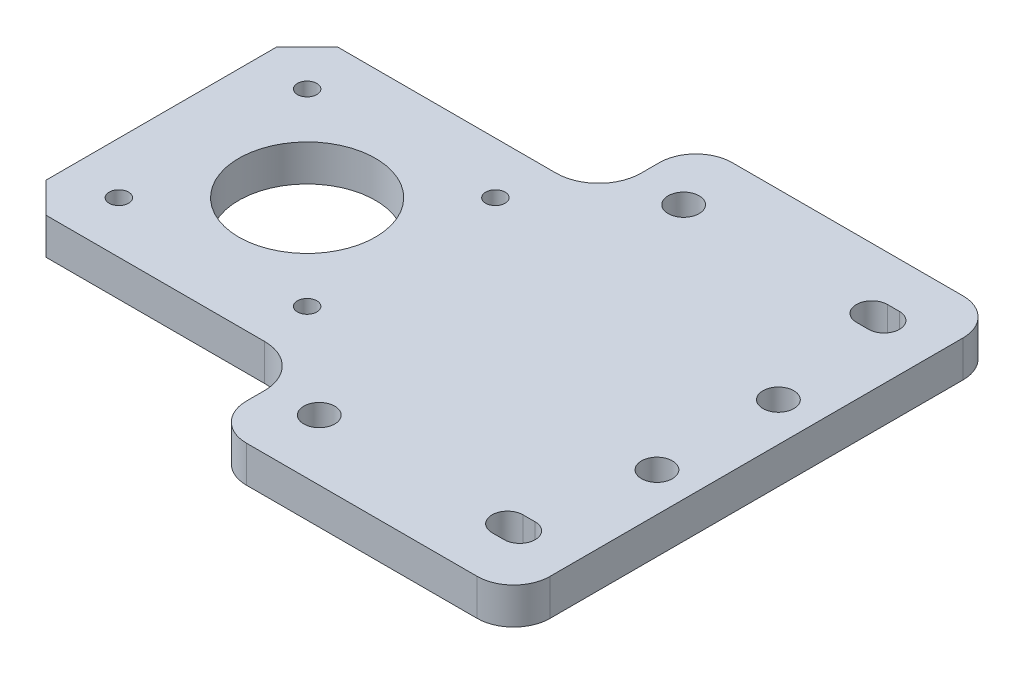
SolidWorks part; units mm, degrees
material "Клен"
ref_plane "Спереди" through (0, 0, 0) normal (0, 0, 1) x (1, 0, 0)
ref_plane "Сверху" through (0, 0, 0) normal (0, 1, 0) x (1, 0, 0)
ref_plane "Справа" through (0, 0, 0) normal (1, 0, 0) x (0, 0, -1)
sketch "Эскиз1" plane through (0, 0, 0) normal (0, 1, 0) x (1, 0, 0)
  line L0 (-56.8562, 0) -> (56.8562, 0) construction
  line L9 (-32, -24) -> (-68, -24)
  line L10 (-19, -40) -> (19, -40)
  line L11 (-25, -34) -> (-25, -31)
  line L12 (-19, 40) -> (19, 40)
  line L13 (25, -34) -> (25, 34)
  line L14 (-25, -40) -> (25, 40) construction
  line L15 (-25, 40) -> (25, -40) construction
  line L20 (-73, -19) -> (-73, 19)
  line L21 (-32, 24) -> (-68, 24)
  line L22 (-25, 31) -> (-25, 34)
  line L23 (-68, -24) -> (-73, -19)
  line L24 (-68, 24) -> (-73, 19)
  line L25 (-73, -24) -> (-25, 24) construction
  line L26 (-25, -24) -> (-72.5248, 23.5248) construction
  line L27 (-49, -29.3961) -> (-49, 34.1878) construction
  line L28 (12.105, -10) -> (440.105, -10) construction
  line L29 (12.105, -10.6243) -> (12.105, -12.7157) construction
  arc A4 (19, 40) -> (25, 34) centre (19, 34) cw
  arc A5 (19, -40) -> (25, -34) centre (19, -34) ccw
  arc A6 (-19, -40) -> (-25, -34) centre (-19, -34) cw
  arc A7 (-25, 34) -> (-19, 40) centre (-19, 34) cw
  circle A8 centre (-49, 0) radius 11.25
  circle A9 centre (-64.5, 15.5) radius 1.6
  circle A10 centre (-64.5, -15.5) radius 1.6
  circle A11 centre (-33.5, 15.5) radius 1.6
  circle A12 centre (-33.5, -15.5) radius 1.6
  arc A13 (-25, -31) -> (-32, -24) centre (-32, -31) ccw
  arc A14 (-32, 24) -> (-25, 31) centre (-32, 31) ccw
  circle A15 centre (18.605, -10) radius 2.55
  circle A16 centre (18.605, 10) radius 2.55
  point P0 (0, 0)
  point P22 (-73, -24)
  point P24 (-73, 24)
  point P25 (-75, 0)
  point P32 (-49, 0)
  point P34 (-49.8171, 0.0009)
  point P35 (-49, 0)
  point P36 (-24.7404, 0.0009)
  point P37 (-49, 0)
  point P39 (-49, 0)
  point P56 (-25, 32.5)
  dimension "D1" = 6
  dimension "D6" = 22.5
  dimension "D7" = 3.2
  dimension "D13" = 7
  dimension "D14" = 7
  dimension "D15" = 5.1
  dimension "D2" = 80
  dimension "D3" = 50
  dimension "D4" = 48
  dimension "D10" = 15.5
  dimension "D11" = 15.5
  dimension "D12" = 15.5
  dimension "D5" = 48
  dimension "D17" = 6.5
extrude "Бобышка-Вытянуть1" add sketch "Эскиз1" along normal blind 6
sketch "Эскиз2" plane through (0, 0, 0) normal (0, -1, 0) x (1, 0, 0)
  line L0 (0, -37.0349) -> (0, 29.2907) construction
  line L1 (16, -30) -> (14, -30) construction
  line L2 (16, -32.55) -> (14, -32.55)
  line L3 (16, -27.45) -> (14, -27.45)
  line L6 (-46.1924, 0) -> (55.6646, 0) construction
  line L7 (16, 30) -> (14, 30) construction
  line L8 (16, 32.55) -> (14, 32.55)
  line L9 (16, 27.45) -> (14, 27.45)
  line L10 (-25, 31) -> (-25, 34) construction
  line L11 (19, -40) -> (-19, -40) construction
  circle A0 centre (-17, -30) radius 2.55
  arc A1 (16, -32.55) -> (16, -27.45) centre (16, -30) ccw
  arc A2 (14, -27.45) -> (14, -32.55) centre (14, -30) ccw
  arc A3 (16, 32.55) -> (16, 27.45) centre (16, 30) cw
  arc A4 (14, 27.45) -> (14, 32.55) centre (14, 30) cw
  circle A5 centre (-17, 30) radius 2.55
  point P7 (15, -30)
  point P12 (15, -32.55)
  point P21 (15, 30)
  dimension "D1" = 5.1
  dimension "D2" = 5.1
  dimension "D3" = 2
  dimension "D4" = 33
  dimension "D5" = 8
  dimension "D6" = 10
extrude "Вырез-Вытянуть1" cut sketch "Эскиз2" against normal through all
equation "\"D2@Эскиз2\"=\"D1@Эскиз2\""
equation "\"D5@Эскиз1\"=\"D4@Эскиз1\""
